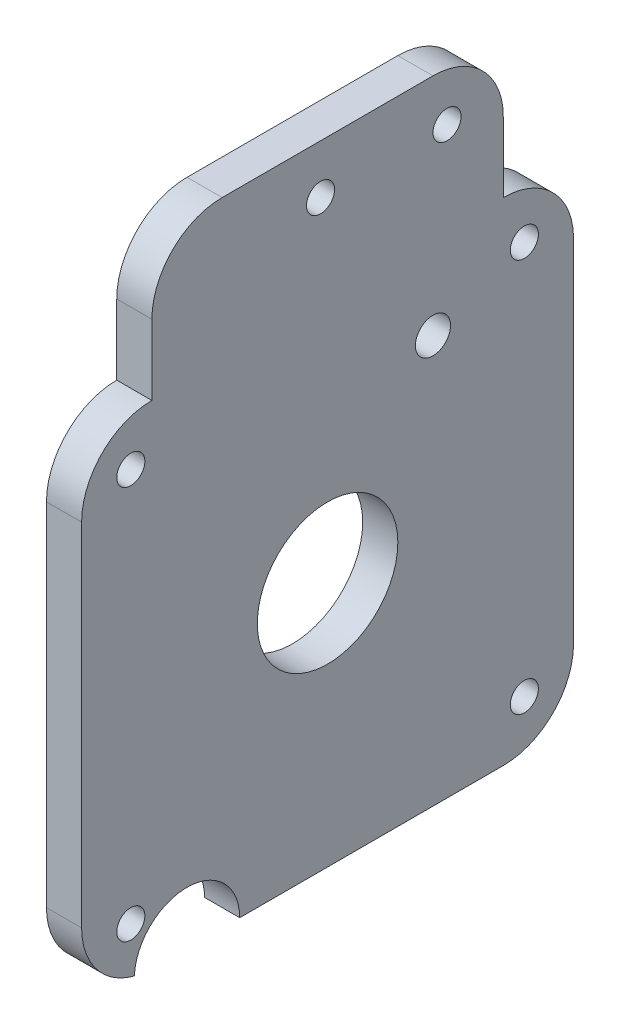
SolidWorks part; units mm, degrees
ref_plane "Alzado" through (0, 0, 0) normal (0, 0, 1) x (1, 0, 0)
ref_plane "Planta" through (0, 0, 0) normal (0, 1, 0) x (1, 0, 0)
ref_plane "Vista lateral" through (0, 0, 0) normal (1, 0, 0) x (0, 0, -1)
sketch "Croquis1" plane through (0, 0, 0) normal (1, 0, 0) x (0, 0, -1)
  line L0 (35, 70) -> (35, 35) construction
  line L1 (10, 0) -> (60, 0)
  line L2 (0, 10) -> (0, 60)
  line L3 (60, 70) -> (10, 70) construction
  line L4 (70, 10) -> (70, 60)
  line L5 (0, 35) -> (35, 35) construction
  line L8 (60, 70) -> (60, 80)
  line L9 (50, 90) -> (20, 90)
  line L10 (10, 70) -> (10, 80)
  arc A0 (10, 0) -> (0, 10) centre (10, 10) cw
  arc A1 (60, 0) -> (70, 10) centre (60, 10) ccw
  arc A2 (60, 70) -> (70, 60) centre (60, 60) cw
  arc A3 (0, 60) -> (10, 70) centre (10, 60) cw
  circle A4 centre (7, 63) radius 2
  circle A5 centre (63, 63) radius 2
  circle A6 centre (63, 7) radius 2
  circle A7 centre (7, 7) radius 2
  circle A8 centre (35, 35) radius 10
  arc A9 (20, 90) -> (10, 80) centre (20, 80) ccw
  arc A10 (60, 80) -> (50, 90) centre (50, 80) ccw
  point P7 (0, 0)
  point P12 (70, 70)
  point P15 (0, 70)
  point P34 (60, 90)
  dimension "D3" = 10
  dimension "D4" = 4
  dimension "D7" = 20
  dimension "D9" = 10
  dimension "D1" = 70
  dimension "D2" = 70
  dimension "D5" = 35
  dimension "D6" = 7
  dimension "D8" = 20
  dimension "D10" = 35
extrude "Saliente-Extruir1" add sketch "Croquis1" along normal blind 5
sketch "Croquis2" plane through (5, 0, 0) normal (1, 0, 0) x (0, 0, -1)
  line L0 (60, 70) -> (10, 70) construction
  line L1 (52, 83) -> (34, 83) construction
  line L2 (10, 0) -> (60, 0) construction
  line L3 (0, 60) -> (0, 10) construction
  line L4 (35, 35) -> (35, 70) construction
  line L5 (60, 70) -> (60, 80) construction
  circle A0 centre (15, 0) radius 7.5
  circle A1 centre (50, 58) radius 2.5
  arc A2 (10, 70) -> (0, 60) centre (10, 60) ccw construction
  circle A3 centre (52, 83) radius 2
  circle A4 centre (34, 83) radius 2
  dimension "D1" = 15
  dimension "D3" = 5
  dimension "D5" = 23
  dimension "D6" = 4
  dimension "D7" = 4
  dimension "D2" = 15
  dimension "D4" = 15
  dimension "D8" = 18
  dimension "D9" = 8
  dimension "D10" = 13
extrude "Cortar-Extruir1" cut sketch "Croquis2" against normal blind 10
